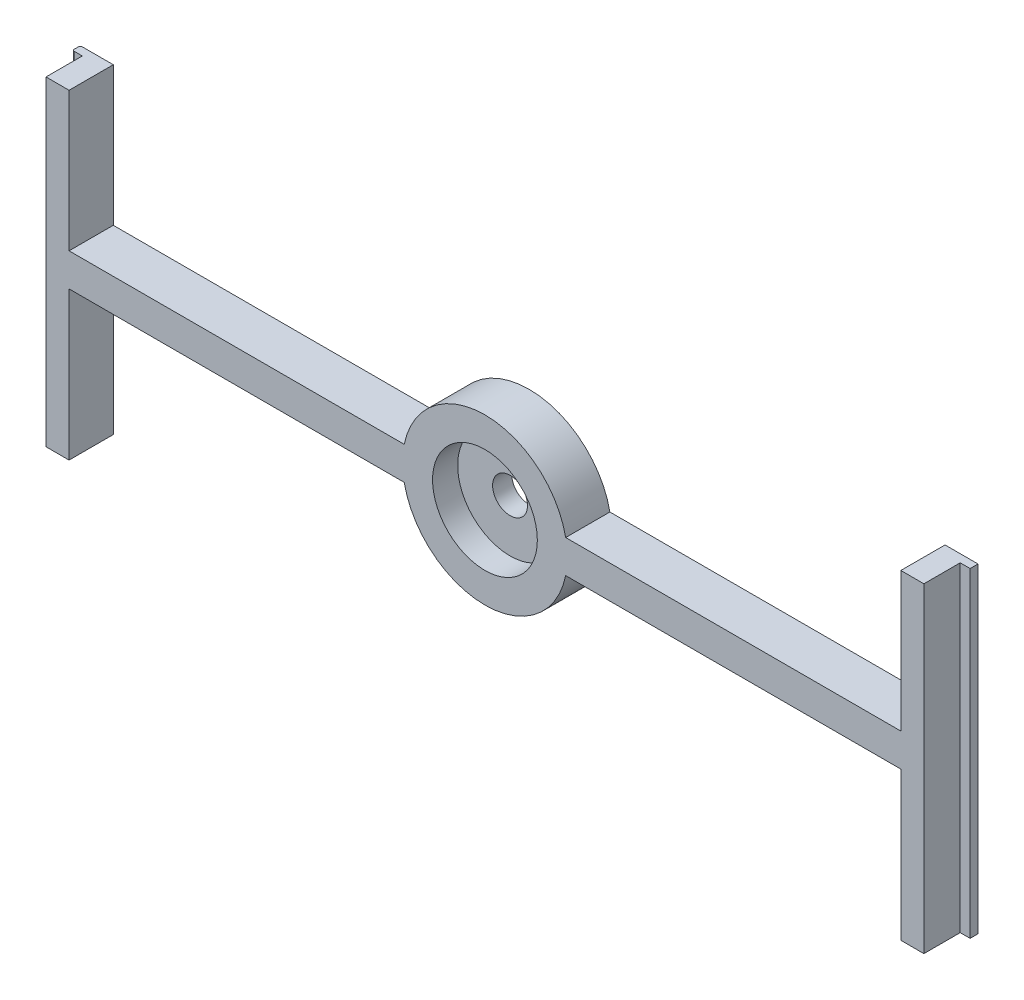
SolidWorks part; units mm, degrees
ref_plane "Front Plane" through (0, 0, 0) normal (0, 0, 1) x (1, 0, 0)
ref_plane "Top Plane" through (0, 0, 0) normal (0, 1, 0) x (1, 0, 0)
ref_plane "Right Plane" through (0, 0, 0) normal (1, 0, 0) x (0, 0, -1)
sketch "Sketch1" plane through (0, 0, 0) normal (0, 0, 1) x (1, 0, 0)
  line L0 (0, 2.5654) -> (0, -2.5654) construction
  line L1 (-63.1, 2.5) -> (-12.2474, 2.5)
  line L3 (-63.1, -2.5) -> (-12.2474, -2.5)
  line L5 (63.1, 25) -> (68.1, 25)
  line L6 (63.1, 25) -> (63.1, 2.5)
  line L7 (63.1, -25) -> (68.1, -25)
  line L8 (68.1, 25) -> (68.1, -25)
  line L9 (-63.1, -25) -> (-68.1, -25)
  line L10 (-68.1, 25) -> (-68.1, -25)
  line L11 (-63.1, 25) -> (-68.1, 25)
  line L12 (-63.1, 25) -> (-63.1, 2.5)
  line L13 (-63.1, -2.5) -> (-63.1, -25)
  line L14 (63.1, -2.5) -> (63.1, -25)
  line L15 (63.1, 2.5) -> (63.1, -2.5) construction
  line L17 (12.2474, 2.5) -> (63.1, 2.5)
  line L18 (12.2474, -2.5) -> (63.1, -2.5)
  arc A6 (-12.2474, -2.5) -> (12.2474, -2.5) centre (0, 0) ccw
  arc A7 (12.2474, 2.5) -> (-12.2474, 2.5) centre (0, 0) ccw
  point P23 (63.1, 0)
  point P24 (0, 0)
  point P25 (-68.1, 0)
  dimension "D6" = 25
  dimension "D1" = 126.2
  dimension "D2" = 5
  dimension "D3" = 50
  dimension "D4" = 5
extrude "Boss-Extrude1" add sketch "Sketch1" along normal blind 6.71
sketch "Sketch2" plane through (0, -25, 0) normal (0, -1, 0) x (1, 0, 0)
  line L0 (63.1, 6.71) -> (68.1, 6.71) construction
  line L5 (66.6, 6.71) -> (68.1, 6.71)
  line L6 (66.6, 6.71) -> (66.6, 1.2)
  line L7 (66.6, 1.2) -> (68.1, 1.2)
  line L8 (68.1, 6.71) -> (68.1, 1.2)
  line L9 (68.1, 6.71) -> (68.1, 0) construction
  line L10 (0, 0) -> (0, -12.1014) construction
  line L20 (40.3185, 1.2) -> (40.3185, 5.51) construction
  line L24 (-68.1, 6.71) -> (-68.1, 1.2)
  line L25 (-66.6, 1.2) -> (-68.1, 1.2)
  line L26 (-66.6, 6.71) -> (-66.6, 1.2)
  line L27 (-66.6, 6.71) -> (-68.1, 6.71)
  line L28 (63.1, 0) -> (68.1, 0) construction
  point P21 (68.1, 3.355)
  point P22 (40.3185, 3.355)
  dimension "D1" = 1.5
  dimension "D2" = 1.2
extrude "Cut-Extrude1" cut sketch "Sketch2" against normal through all
sketch "Sketch3" plane through (0, 0, 6.71) normal (0, 0, 1) x (1, 0, 0)
  circle A2 centre (0, 0) radius 7.9502
  point P0 (0, 0)
  dimension "D1" = 15.9004
extrude "Cut-Extrude2" cut sketch "Sketch3" against normal blind 3.81
sketch "Sketch4" plane through (0, 0, 6.71) normal (0, 0, 1) x (1, 0, 0)
  line L0 (68.1, 25) -> (68.1, -25) construction
  line L1 (-68.1, 25) -> (68.1, 25)
  line L2 (-68.1, 25) -> (-68.1, 23.6)
  line L3 (-68.1, 23.6) -> (68.1, 23.6)
  line L4 (68.1, 25) -> (68.1, 23.6)
  dimension "D1" = 1.4
extrude "Cut-Extrude3" cut sketch "Sketch4" against normal through all
sketch "Sketch5" plane through (0, 0, 2.9) normal (0, 0, 1) x (1, 0, 0)
  circle A0 centre (0, 0) radius 2.65
  dimension "D1" = 5.3
extrude "Cut-Extrude4" cut sketch "Sketch5" against normal through all
fillet "Fillet1" radius 0.3 2 edges at (-68.1, -0.7, 0) (-68.1, -0.7, 1.2)
